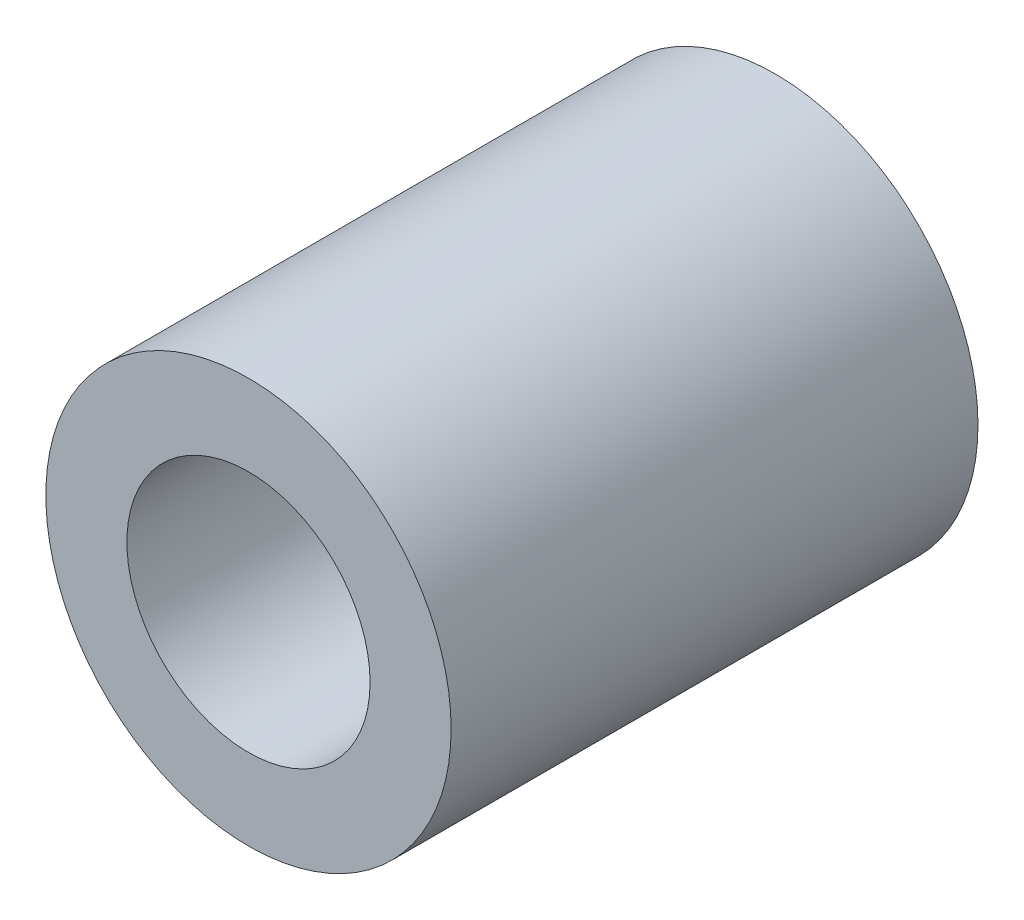
SolidWorks part; units mm, degrees
ref_plane "Plan de face" through (0, 0, 0) normal (0, 0, 1) x (1, 0, 0)
ref_plane "Plan de dessus" through (0, 0, 0) normal (0, 1, 0) x (1, 0, 0)
ref_plane "Plan de droite" through (0, 0, 0) normal (1, 0, 0) x (0, 0, -1)
sketch "Esquisse1" plane through (0, 0, 0) normal (0, 0, 1) x (1, 0, 0)
  circle A0 centre (0, 0) radius 3
  circle A1 centre (0, 0) radius 5
extrude "Extrusion1" add sketch "Esquisse1" along normal blind 13
